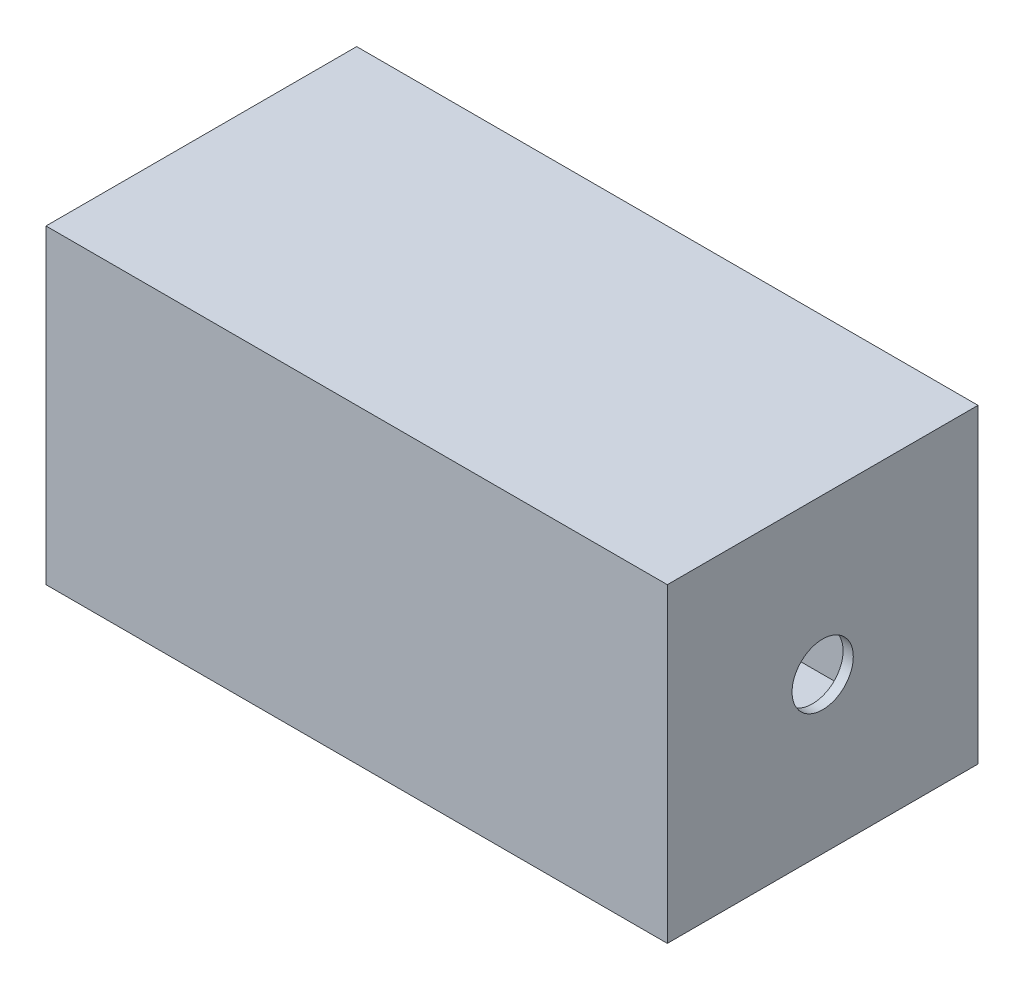
SolidWorks part; units mm, degrees
ref_plane "Front Plane" through (0, 0, 0) normal (0, 0, 1) x (1, 0, 0)
ref_plane "Top Plane" through (0, 0, 0) normal (0, 1, 0) x (1, 0, 0)
ref_plane "Right Plane" through (0, 0, 0) normal (1, 0, 0) x (0, 0, -1)
sketch "Sketch1" plane through (0, 0, 0) normal (0, 1, 0) x (1, 0, 0)
  line L1 (-305, 152.5) -> (305, 152.5)
  line L2 (-305, 152.5) -> (-305, -152.5)
  line L3 (-305, -152.5) -> (305, -152.5)
  line L4 (305, 152.5) -> (305, -152.5)
  line L5 (-305, 152.5) -> (305, -152.5) construction
  line L6 (-305, -152.5) -> (305, 152.5) construction
  point P0 (0, 0)
  dimension "D1" = 610
  dimension "D2" = 305
extrude "Boss-Extrude1" add sketch "Sketch1" along normal blind 305
shell "Shell1" thickness 10
sketch "Sketch2" plane through (305, 0, 0) normal (1, 0, 0) x (0, 0, -1)
  line L0 (0, 305) -> (0, 0) construction
  line L1 (-152.5, 305) -> (152.5, 305) construction
  line L2 (-152.5, 152.5) -> (152.5, 152.5) construction
  line L3 (-152.5, 305) -> (-152.5, 0) construction
  line L4 (152.5, 305) -> (152.5, 0) construction
  circle A0 centre (0, 152.5) radius 30.0753
extrude "Cut-Extrude1" cut sketch "Sketch2" against normal up to next
